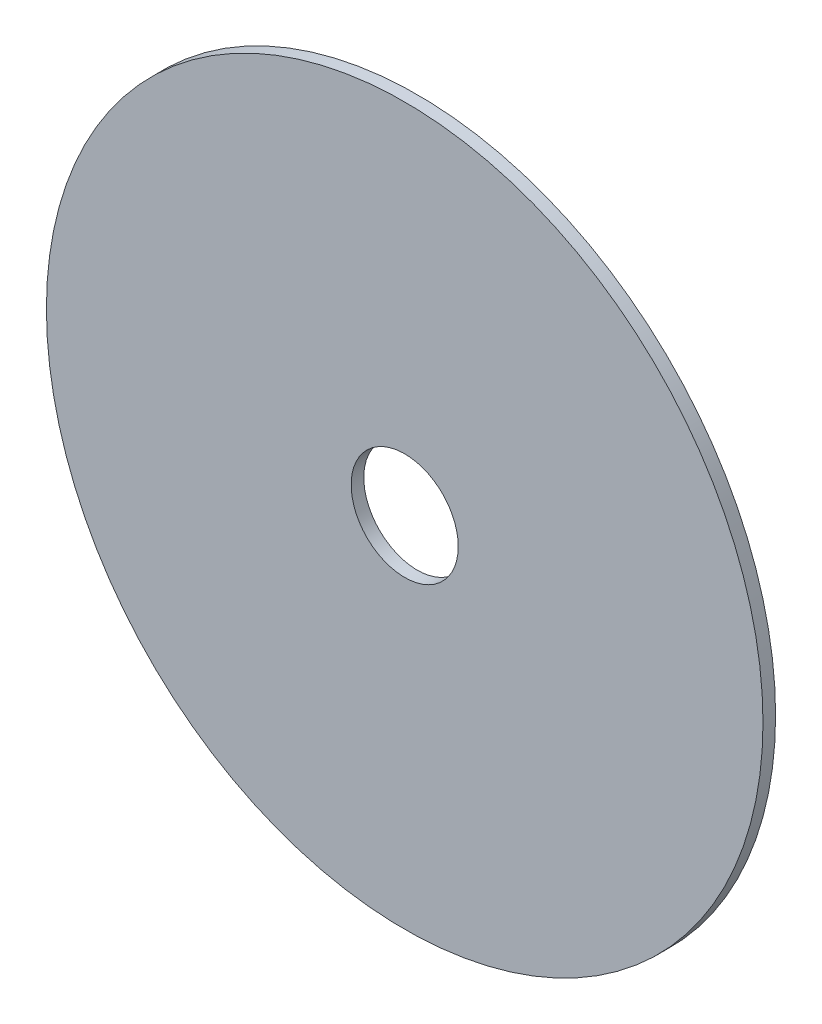
SolidWorks part; units mm, degrees
ref_plane "Face" through (0, 0, 0) normal (0, 0, 1) x (1, 0, 0)
ref_plane "Dessus" through (0, 0, 0) normal (0, 1, 0) x (1, 0, 0)
ref_plane "Cote" through (0, 0, 0) normal (1, 0, 0) x (0, 0, -1)
sketch "Esquisse1" plane through (0, 0, 0) normal (0, 0, 1) x (1, 0, 0)
  circle A0 centre (0, 0) radius 22.75
  circle A1 centre (0, 0) radius 3.4
  dimension "D1" = 45.5
  dimension "D2" = 6.8
extrude "Base-Extrusion" add sketch "Esquisse1" against normal blind 0.8
equation "\"dummy\"= iif ( \"true\" , \"part.configurationmanager.activeconfiguration.custompropertymanager.delete\" ( \"let\"\" & \"\"tre\" )  , \"part.configurationmanager.activeconfiguration.custompropertymanager.add2\" ( \"let\"\" & \"\"tre\" , 30 ,  left ( \"part.configurationmanager.activeconfiguration.name\" , 1 )  )  ) "
